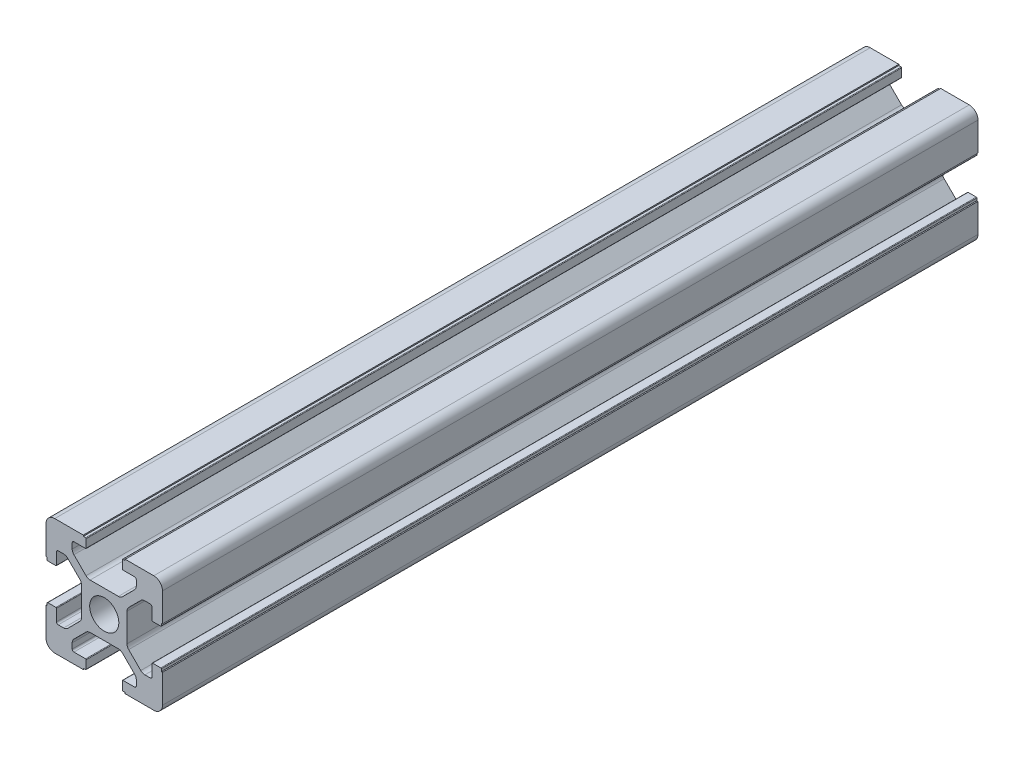
SolidWorks part; units mm, degrees
material "6063-T5"
ref_plane "前视基准面" through (0, 0, 0) normal (0, 0, 1) x (1, 0, 0)
ref_plane "上视基准面" through (0, 0, 0) normal (0, 1, 0) x (1, 0, 0)
ref_plane "右视基准面" through (0, 0, 0) normal (1, 0, 0) x (0, 0, -1)
sketch "草图1" plane through (0, 0, 0) normal (0, 0, 1) x (1, 0, 0)
  line L0 (-1.4389, 10) -> (24.3741, 10) construction
  line L1 (20, 13.6) -> (20, 20)
  line L2 (0, 0) -> (0, 6.4)
  line L3 (0, 20) -> (6.4, 20)
  line L4 (20, 0) -> (20, 6.4)
  line L5 (10, 21.5388) -> (10, -2.4017) construction
  line L6 (6.9, 18.3) -> (6.9, 19.7)
  line L7 (6.8, 18.2) -> (4.8, 18.2)
  line L8 (4.5, 17.9) -> (4.5, 16.9749)
  line L9 (4.7929, 16.2678) -> (6.8678, 14.1929)
  line L10 (7.5749, 13.9) -> (12.4251, 13.9)
  line L11 (6.8, 19.8) -> (6.4, 19.8)
  line L12 (6.4, 19.8) -> (6.4, 20)
  line L13 (0, 13.6) -> (0.2, 13.6)
  line L14 (0.2, 13.6) -> (0.2, 13.2)
  line L15 (0.3, 13.1) -> (1.7, 13.1)
  line L16 (1.8, 13.2) -> (1.8, 15.2)
  line L17 (2.1, 15.5) -> (3.0251, 15.5)
  line L18 (3.7322, 15.2071) -> (5.8071, 13.1322)
  line L19 (6.1, 12.4251) -> (6.1, 7.5749)
  line L20 (13.6, 19.8) -> (13.6, 20)
  line L21 (13.2, 19.8) -> (13.6, 19.8)
  line L22 (13.1, 18.3) -> (13.1, 19.7)
  line L23 (13.2, 18.2) -> (15.2, 18.2)
  line L24 (15.5, 17.9) -> (15.5, 16.9749)
  line L25 (15.2071, 16.2678) -> (13.1322, 14.1929)
  line L26 (0, 6.4) -> (0.2, 6.4)
  line L27 (0.2, 6.4) -> (0.2, 6.8)
  line L28 (0.3, 6.9) -> (1.7, 6.9)
  line L29 (1.8, 6.8) -> (1.8, 4.8)
  line L30 (2.1, 4.5) -> (3.0251, 4.5)
  line L31 (3.7322, 4.7929) -> (5.8071, 6.8678)
  line L32 (13.6, 20) -> (20, 20)
  line L33 (0, 13.6) -> (0, 20)
  line L34 (13.6, 0.2) -> (13.6, 0)
  line L35 (13.2, 0.2) -> (13.6, 0.2)
  line L36 (13.1, 1.7) -> (13.1, 0.3)
  line L37 (13.2, 1.8) -> (15.2, 1.8)
  line L38 (15.5, 2.1) -> (15.5, 3.0251)
  line L39 (15.2071, 3.7322) -> (13.1322, 5.8071)
  line L40 (4.5, 2.1) -> (4.5, 3.0251)
  line L41 (6.8, 1.8) -> (4.8, 1.8)
  line L42 (6.4, 0.2) -> (6.4, 0)
  line L43 (6.8, 0.2) -> (6.4, 0.2)
  line L44 (6.9, 1.7) -> (6.9, 0.3)
  line L45 (4.7929, 3.7322) -> (6.8678, 5.8071)
  line L46 (7.5749, 6.1) -> (12.4251, 6.1)
  line L47 (20, 6.4) -> (19.8, 6.4)
  line L48 (19.8, 6.4) -> (19.8, 6.8)
  line L49 (19.7, 6.9) -> (18.3, 6.9)
  line L50 (18.2, 6.8) -> (18.2, 4.8)
  line L51 (17.9, 4.5) -> (16.9749, 4.5)
  line L52 (16.2678, 4.7929) -> (14.1929, 6.8678)
  line L53 (13.9, 12.4251) -> (13.9, 7.5749)
  line L54 (16.2678, 15.2071) -> (14.1929, 13.1322)
  line L55 (17.9, 15.5) -> (16.9749, 15.5)
  line L56 (18.2, 13.2) -> (18.2, 15.2)
  line L57 (19.7, 13.1) -> (18.3, 13.1)
  line L58 (19.8, 13.6) -> (19.8, 13.2)
  line L59 (20, 13.6) -> (19.8, 13.6)
  line L60 (0, 0) -> (6.4, 0)
  line L61 (13.6, 0) -> (20, 0)
  arc A0 (6.1, 12.4251) -> (5.8071, 13.1322) centre (5.1, 12.4251) ccw
  arc A1 (7.5749, 13.9) -> (6.8678, 14.1929) centre (7.5749, 14.9) cw
  arc A2 (4.5, 16.9749) -> (4.7929, 16.2678) centre (5.5, 16.9749) ccw
  arc A3 (3.7322, 15.2071) -> (3.0251, 15.5) centre (3.0251, 14.5) ccw
  arc A4 (4.5, 17.9) -> (4.8, 18.2) centre (4.8, 17.9) cw
  arc A5 (1.8, 15.2) -> (2.1, 15.5) centre (2.1, 15.2) cw
  arc A6 (0.3, 13.1) -> (0.2, 13.2) centre (0.3, 13.2) cw
  arc A7 (6.9, 19.7) -> (6.8, 19.8) centre (6.8, 19.7) ccw
  arc A8 (1.7, 13.1) -> (1.8, 13.2) centre (1.7, 13.2) ccw
  arc A9 (6.9, 18.3) -> (6.8, 18.2) centre (6.8, 18.3) cw
  arc A10 (13.1, 19.7) -> (13.2, 19.8) centre (13.2, 19.7) cw
  arc A11 (13.1, 18.3) -> (13.2, 18.2) centre (13.2, 18.3) ccw
  arc A12 (15.5, 17.9) -> (15.2, 18.2) centre (15.2, 17.9) ccw
  arc A13 (15.5, 16.9749) -> (15.2071, 16.2678) centre (14.5, 16.9749) cw
  arc A14 (12.4251, 13.9) -> (13.1322, 14.1929) centre (12.4251, 14.9) ccw
  arc A15 (0.3, 6.9) -> (0.2, 6.8) centre (0.3, 6.8) ccw
  arc A16 (1.7, 6.9) -> (1.8, 6.8) centre (1.7, 6.8) cw
  arc A17 (1.8, 4.8) -> (2.1, 4.5) centre (2.1, 4.8) ccw
  arc A18 (3.7322, 4.7929) -> (3.0251, 4.5) centre (3.0251, 5.5) cw
  arc A19 (6.1, 7.5749) -> (5.8071, 6.8678) centre (5.1, 7.5749) cw
  arc A20 (13.1, 0.3) -> (13.2, 0.2) centre (13.2, 0.3) ccw
  arc A21 (13.1, 1.7) -> (13.2, 1.8) centre (13.2, 1.7) cw
  arc A22 (15.5, 2.1) -> (15.2, 1.8) centre (15.2, 2.1) cw
  arc A23 (15.5, 3.0251) -> (15.2071, 3.7322) centre (14.5, 3.0251) ccw
  arc A24 (12.4251, 6.1) -> (13.1322, 5.8071) centre (12.4251, 5.1) cw
  arc A25 (4.5, 2.1) -> (4.8, 1.8) centre (4.8, 2.1) ccw
  arc A26 (6.9, 0.3) -> (6.8, 0.2) centre (6.8, 0.3) cw
  arc A27 (6.9, 1.7) -> (6.8, 1.8) centre (6.8, 1.7) ccw
  arc A28 (4.5, 3.0251) -> (4.7929, 3.7322) centre (5.5, 3.0251) cw
  arc A29 (7.5749, 6.1) -> (6.8678, 5.8071) centre (7.5749, 5.1) ccw
  arc A30 (19.7, 6.9) -> (19.8, 6.8) centre (19.7, 6.8) cw
  arc A31 (18.3, 6.9) -> (18.2, 6.8) centre (18.3, 6.8) ccw
  arc A32 (18.2, 4.8) -> (17.9, 4.5) centre (17.9, 4.8) cw
  arc A33 (16.2678, 4.7929) -> (16.9749, 4.5) centre (16.9749, 5.5) ccw
  arc A34 (13.9, 7.5749) -> (14.1929, 6.8678) centre (14.9, 7.5749) ccw
  arc A35 (13.9, 12.4251) -> (14.1929, 13.1322) centre (14.9, 12.4251) cw
  arc A36 (16.2678, 15.2071) -> (16.9749, 15.5) centre (16.9749, 14.5) cw
  arc A37 (18.2, 15.2) -> (17.9, 15.5) centre (17.9, 15.2) ccw
  arc A38 (18.3, 13.1) -> (18.2, 13.2) centre (18.3, 13.2) cw
  arc A39 (19.7, 13.1) -> (19.8, 13.2) centre (19.7, 13.2) ccw
  circle A40 centre (10, 10) radius 2.5
  point P39 (0.2, 13.1)
  point P42 (6.9, 19.8)
  point P45 (1.8, 13.1)
  point P48 (6.9, 18.2)
  point P66 (10, 13.9)
  point P83 (6.1, 10)
  dimension "D19" = 1
  dimension "D20" = 1
  dimension "D21" = 0.3
  dimension "D22" = 0.1
  dimension "D23" = 5
  dimension "D1" = 20
  dimension "D2" = 20
  dimension "D3" = 10
  dimension "D4" = 10
  dimension "D5" = 1.8
  dimension "D6" = 0.5
  dimension "D7" = 1.6
  dimension "D8" = 3.1
  dimension "D9" = 6.1
  dimension "D10" = 5.5
  dimension "D11" = 3.1
  dimension "D12" = 6.1
  dimension "D13" = 5.5
  dimension "D14" = 1.8
  dimension "D15" = 0.5
  dimension "D16" = 1.5
  dimension "D17" = 45
  dimension "D18" = 1.6
extrude "凸台-拉伸1" add sketch "草图1" along normal blind 140
fillet "圆角1" radius 1.5 4 edges at (20, 0, 70) (0, 0, 70) (0, 20, 70) (20, 20, 70)
